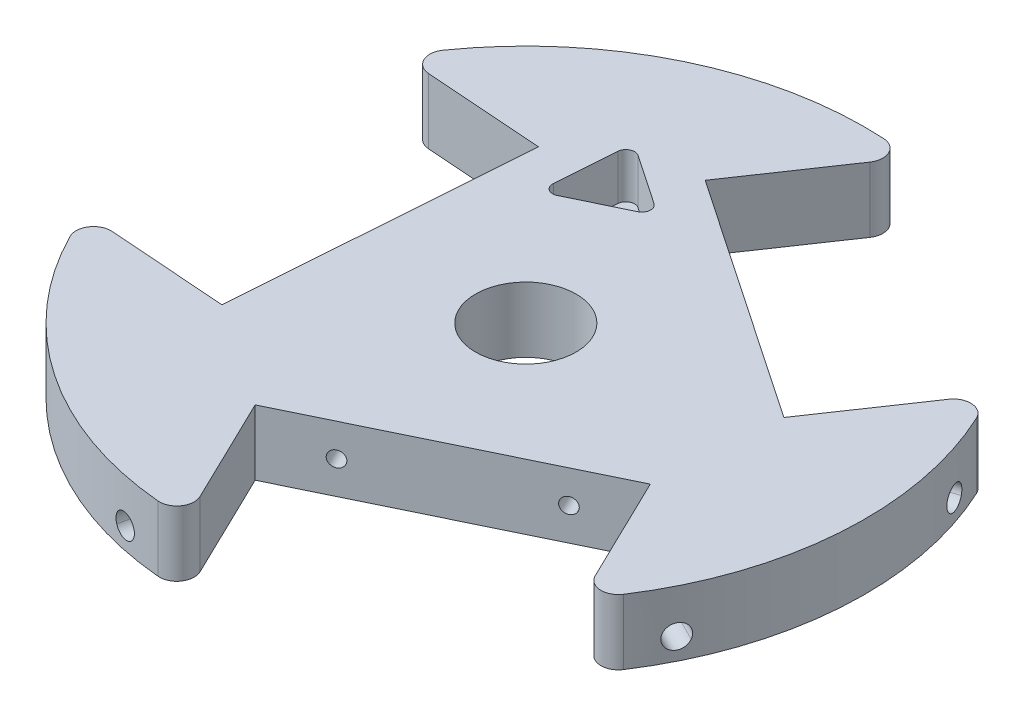
SolidWorks part; units mm, degrees
material "6061-T6 (SS)"
ref_plane "Front Plane" through (0, 0, 0) normal (0, 0, 1) x (1, 0, 0)
ref_plane "Top Plane" through (0, 0, 0) normal (0, 1, 0) x (1, 0, 0)
ref_plane "Right Plane" through (0, 0, 0) normal (1, 0, 0) x (0, 0, -1)
sketch "Sketch1" plane through (0, 0, 0) normal (0, 1, 0) x (1, 0, 0)
  line L0 (0, -49.53) -> (-9.411, -30.0991)
  line L5 (-9.411, -30.0991) -> (29.4508, -11.277)
  line L6 (29.4508, -11.277) -> (38.8618, -30.7079)
  line L7 (-42.8942, 24.765) -> (-21.3611, 23.1997)
  line L8 (-21.3611, 23.1997) -> (-24.4916, -19.8666)
  line L9 (-24.4916, -19.8666) -> (-46.0248, -18.3014)
  line L10 (42.8942, 24.765) -> (30.7721, 6.8994)
  line L11 (30.7721, 6.8994) -> (-4.9592, 31.1437)
  line L12 (-4.9592, 31.1437) -> (7.1629, 49.0093)
  circle A0 centre (0, 0) radius 49.53
  point P4 (0, -49.53)
  point P5 (38.8618, -30.7079)
  point P12 (-42.8942, 24.765)
  point P13 (-46.0248, -18.3014)
  point P18 (42.8942, 24.765)
  point P19 (7.1629, 49.0093)
  point P24 (0, 0)
  dimension "D3" = 99.06
  dimension "D2" = 21.59
  dimension "D4" = 43.18
  dimension "D1" = 3
extrude "Boss-Extrude1" add sketch "Sketch1" along normal blind 9.525
hole_wizard "5/8-18 Tapped Hole1" positions "Sketch2" profile "Sketch3" tap size "5/8-18" standard "ANSI Inch" end condition through all
sketch "Sketch2" plane through (0, 9.525, 0) normal (0, 1, 0) x (1, 0, 0)
  point P0 (0, 0)
sketch "Sketch3" plane through (0, 9.525, 0) normal (1, 0, 0) x (0, 0, 1)
  line L0 (0, 0) -> (0, 9.525)
  line L1 (0, 9.525) -> (7.3419, 9.525)
  line L2 (7.3419, 9.525) -> (7.3419, 0)
  line L5 (7.3419, 0) -> (0, 0)
  line L11 (0, -6.35) -> (0, 107.95) construction
  dimension "Thru Tap Drill Dia." = 14.6837
  dimension "Thru Tap Drill Depth" = 9.525
cosmetic thread "Hole Thread1" parameters "D2"=15.875
fillet "Fillet1" radius 2.54 6 edges at (7.1629, 4.7625, -49.0093) (42.8942, 4.7625, -24.765) (38.8618, 4.7625, 30.7079) (0, 4.7625, 49.53) (-46.0248, 4.7625, 18.3014) (-42.8942, 4.7625, -24.765)
sketch "Sketch4" plane through (-22.9263, 0, -1.6665) normal (-0.9974, 0, -0.0725) x (-0.0725, 0, 0.9974)
  line L0 (-21.59, 9.525) -> (21.59, 9.525) construction
  line L1 (0, 9.525) -> (0, 0) construction
  line L2 (-21.59, 0) -> (21.59, 0) construction
  line L3 (-21.59, 9.525) -> (-21.59, 0) construction
  line L4 (-21.59, 4.7625) -> (0, 4.7625) construction
  point P0 (0, 9.525)
  point P7 (-21.59, 4.7625)
  point P12 (-12.7, 4.7625)
  point P13 (12.7, 4.7625)
  dimension "D1" = 12.7
hole_wizard "#4-40 Tapped Hole1" positions "Sketch5" profile "Sketch6" tap size "#4-40" standard "ANSI Inch"
sketch "Sketch5" plane through (-22.9263, 0, -1.6665) normal (-0.9974, 0, -0.0725) x (-0.0725, 0, 0.9974)
  point P0 (-12.7, 4.7625)
  point P3 (12.7, 4.7625)
sketch "Sketch6" plane through (-22.0056, 4.7625, -14.3331) normal (0, 1, 0) x (-0.0725, 0, 0.9974)
  line L0 (0, 0) -> (0, 7.0292)
  line L1 (0, 7.0292) -> (1.1303, 6.35)
  line L2 (1.1303, 6.35) -> (1.1303, 0)
  line L5 (1.1303, 0) -> (0, 0)
  line L10 (0, 7.0292) -> (-1.1303, 6.35) construction
  line L11 (0, -6.35) -> (0, 107.95) construction
  dimension "Tap Drill Dia." = 2.2606
  dimension "Tap Drill Depth" = 6.35
  dimension "Drill Angle" = 118
sketch "Sketch7" plane through (10.0199, 0, 20.6881) normal (0.4359, 0, 0.9) x (0.9, 0, -0.4359)
  line L0 (0, 9.525) -> (0, 0) construction
  line L1 (-21.59, 9.525) -> (21.59, 9.525) construction
  line L2 (-21.59, 0) -> (21.59, 0) construction
  line L3 (-21.59, 4.7625) -> (0, 4.7625) construction
  line L4 (-21.59, 9.525) -> (-21.59, 0) construction
  point P10 (-12.7, 4.7625)
  point P11 (12.7, 4.7625)
  dimension "D1" = 12.7
hole_wizard "#4-40 Tapped Hole2" positions "Sketch8" profile "Sketch9" tap size "#4-40" standard "ANSI Inch"
sketch "Sketch8" plane through (10.0199, 0, 20.6881) normal (0.4359, 0, 0.9) x (0.9, 0, -0.4359)
  point P0 (-12.7, 4.7625)
  point P3 (12.7, 4.7625)
sketch "Sketch9" plane through (-1.4101, 4.7625, 26.224) normal (0, 1, 0) x (0.9, 0, -0.4359)
  line L0 (0, 0) -> (0, 7.0292)
  line L1 (0, 7.0292) -> (1.1303, 6.35)
  line L2 (1.1303, 6.35) -> (1.1303, 0)
  line L5 (1.1303, 0) -> (0, 0)
  line L10 (0, 7.0292) -> (-1.1303, 6.35) construction
  line L11 (0, -6.35) -> (0, 107.95) construction
  dimension "Tap Drill Dia." = 2.2606
  dimension "Tap Drill Depth" = 6.35
  dimension "Drill Angle" = 118
sketch "Sketch10" plane through (12.9064, 0, -19.0215) normal (0.5615, 0, -0.8275) x (-0.8275, 0, -0.5615)
  line L0 (0, 9.525) -> (0, 0) construction
  line L1 (-21.59, 9.525) -> (21.59, 9.525) construction
  line L2 (-21.59, 0) -> (21.59, 0) construction
  line L3 (-21.59, 4.7625) -> (0, 4.7625) construction
  line L4 (-21.59, 9.525) -> (-21.59, 0) construction
  point P10 (-12.7, 4.7625)
  point P11 (12.7, 4.7625)
  dimension "D1" = 12.7
hole_wizard "#4-40 Tapped Hole3" positions "Sketch11" profile "Sketch12" tap size "#4-40" standard "ANSI Inch"
sketch "Sketch11" plane through (12.9064, 0, -19.0215) normal (0.5615, 0, -0.8275) x (-0.8275, 0, -0.5615)
  point P0 (-12.7, 4.7625)
  point P3 (12.7, 4.7625)
sketch "Sketch12" plane through (23.4156, 4.7625, -11.8908) normal (0, 1, 0) x (-0.8275, 0, -0.5615)
  line L0 (0, 0) -> (0, 7.0292)
  line L1 (0, 7.0292) -> (1.1303, 6.35)
  line L2 (1.1303, 6.35) -> (1.1303, 0)
  line L5 (1.1303, 0) -> (0, 0)
  line L10 (0, 7.0292) -> (-1.1303, 6.35) construction
  line L11 (0, -6.35) -> (0, 107.95) construction
  dimension "Tap Drill Dia." = 2.2606
  dimension "Tap Drill Depth" = 6.35
  dimension "Drill Angle" = 118
sketch "Sketch14" plane through (0, 9.525, 0) normal (0, 1, 0) x (1, 0, 0)
  line L0 (0, 0) -> (-27.8097, -40.9859)
  line L1 (0, 0) -> (-10.0081, -48.5083)
  line L2 (0, 0) -> (-41.3774, -27.2237)
  arc A0 (-44.2329, -22.2861) -> (-4.3648, -49.3373) centre (0, 0) ccw construction
  point P0 (-27.8097, -40.9859)
  point P1 (-72.1861, 9.8914)
  dimension "D1" = 22.5
ref_plane "Plane1" through (-10.0081, 9.525, 48.5083) normal (-0.2021, 0, 0.9794) x (0.9794, 0, 0.2021)
sketch "Sketch16" plane through (-10.0081, 9.525, 48.5083) normal (-0.2021, 0, 0.9794) x (0.9794, 0, 0.2021)
  line L0 (0, -0.0192) -> (0, -9.525)
  point P5 (0, -4.7721)
ref_plane "Plane2" through (-41.3774, 0, 27.2237) normal (-0.8354, 0, 0.5496) x (0.5496, 0, 0.8354)
sketch "Sketch17" plane through (-41.3774, 0, 27.2237) normal (-0.8354, 0, 0.5496) x (0.5496, 0, 0.8354)
  line L0 (0, 6.3036) -> (0, 0)
  point P3 (0, 3.1518)
hole_wizard "#8-32 Tapped Hole1" positions "Sketch18" profile "Sketch19" tap size "#8-32" standard "ANSI Inch"
sketch "Sketch18" plane through (-41.3774, 0, 27.2237) normal (-0.8354, 0, 0.5496) x (0.5496, 0, 0.8354)
  point P0 (0, 3.1518)
sketch "Sketch19" plane through (-41.3774, 3.1518, 27.2237) normal (0, 1, 0) x (0.5496, 0, 0.8354)
  line L0 (0, 0) -> (0, 7.3878)
  line L1 (0, 7.3878) -> (1.7272, 6.35)
  line L2 (1.7272, 6.35) -> (1.7272, 0)
  line L5 (1.7272, 0) -> (0, 0)
  line L10 (0, 7.3878) -> (-1.7272, 6.35) construction
  line L11 (0, -6.35) -> (0, 107.95) construction
  dimension "Tap Drill Dia." = 3.4544
  dimension "Tap Drill Depth" = 6.35
  dimension "Drill Angle" = 118
ref_plane "Plane4" through (0, 0, 0) normal (-0.8275, 0, -0.5615) x (-0.5615, 0, 0.8275)
mirror "Mirror1" about plane through (0, 0, 0) normal (-0.8275, 0, -0.5615) of "#8-32 Tapped Hole1"
pattern_circular "CirPattern1" count 3 over 360 about axis through (0, 9.525, 0) along (0, 1, 0) of "#8-32 Tapped Hole1", "Mirror1"
sketch "Sketch21" plane through (-41.3774, 0, 27.2237) normal (-0.8354, 0, 0.5496) x (0.5496, 0, 0.8354)
  line L0 (0, 3.1518) -> (0, 0)
  line L1 (-1.5735, 2.4396) -> (1.5735, 2.4396)
  line L2 (-5.6944, 0) -> (38.8173, 0) construction
  circle A1 centre (0, 3.1518) radius 3.175
  circle A2 centre (0, 3.1518) radius 1.7272
  circle A3 centre (0, 3.1518) radius 1.7272
  point P11 (-3.175, 3.1518)
  point P12 (3.175, 3.1518)
  point P13 (-3.175, 3.1518)
  dimension "D4" = 6.35
  dimension "D2" = 3.1471
  dimension "D3" = 2.4396
  dimension "D1" = 0
ref_plane "Plane5" through (0, 2.4384, 0) normal (0, -1, 0) x (-1, 0, 0)
split line "Split Line1"
sketch "Sketch20" plane through (0, 9.525, 0) normal (0, 1, 0) x (1, 0, 0)
  line L0 (0, 0) -> (-21.59, 44.5768) construction
  line L2 (-14.9957, 28.4384) -> (-15.6336, 19.6627)
  line L3 (-13.8133, 18.4276) -> (-5.8944, 22.263)
  line L4 (-5.735, 24.4569) -> (-13.016, 29.3972)
  line L5 (-14.9159, 29.5353) -> (-16.1333, 12.7884)
  line L6 (-12.4928, 10.3183) -> (-0.3505, 16.1992)
  line L7 (-0.0315, 20.587) -> (-13.9261, 30.0147)
  arc A0 (2.8161, 49.4499) -> (-40.5449, 28.4487) centre (0, 0) ccw construction
  circle A1 centre (-11.5147, 23.7743) radius 3.81
  circle A2 centre (-11.5147, 23.7743) radius 3.81 construction
  arc A3 (-5.8944, 22.263) -> (-5.735, 24.4569) centre (-6.448, 23.406) ccw
  arc A4 (-14.9957, 28.4384) -> (-13.016, 29.3972) centre (-13.729, 28.3463) cw
  arc A5 (-15.6336, 19.6627) -> (-13.8133, 18.4276) centre (-14.3669, 19.5706) ccw
  circle A6 centre (-9.2265, 19.0499) radius 6.4347 construction
  circle A7 centre (0, 0) radius 14.732 construction
  arc A8 (-16.1333, 12.7884) -> (-12.4928, 10.3183) centre (-13.6, 12.6043) ccw
  arc A9 (-0.3505, 16.1992) -> (-0.0315, 20.587) centre (-1.4577, 18.4852) ccw
  arc A10 (-14.9159, 29.5353) -> (-13.9261, 30.0147) centre (-14.2826, 29.4893) cw
  point P17 (-14.8362, 30.6323)
  point P31 (-14.8362, 30.6323)
  dimension "D1" = 7.62
  dimension "D3" = 1.27
  dimension "D4" = 29.464
  dimension "D5" = 2.54
  dimension "D6" = 0.635
  dimension "D2" = 26.416
extrude "Cut-Extrude5" cut sketch "Sketch20" against normal blind 6.604 contours L5 A5 L3 A1 | A1 | L3 A3 L4 A1 | A4 L2 A1 L7
sketch "Sketch25" plane through (-22.9263, 0, -1.6665) normal (-0.9974, 0, -0.0725) x (-0.0725, 0, 0.9974)
  line L0 (-12.7, 4.7625) -> (-12.7, 0) construction
  line L1 (-21.59, 0) -> (21.59, 0) construction
  line L2 (-13.4681, 3.9333) -> (-11.9319, 3.9333)
  line L3 (-12.7, 4.7625) -> (-12.7, 3.9333)
  circle A2 centre (-12.7, 4.7625) radius 1.1303
  circle A3 centre (-12.7, 4.7625) radius 1.1303
  dimension "D3" = 2.2606
  dimension "D2" = 0.8292
  dimension "D4" = 3.9333
  dimension "D1" = 0
ref_plane "Plane6" through (0, 2.3458, 0) normal (0, -1, 0) x (-1, 0, 0)
split line "Split Line2"
